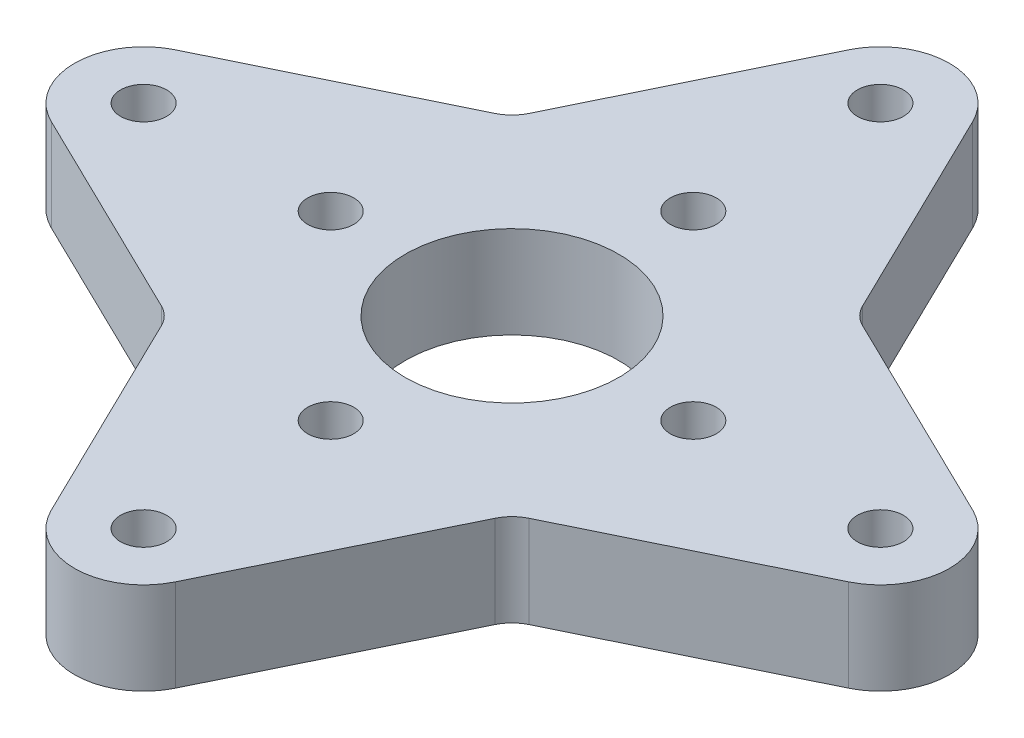
SolidWorks part; units mm, degrees
ref_plane "Front Plane" through (0, 0, 0) normal (0, 0, 1) x (1, 0, 0)
ref_plane "Top Plane" through (0, 0, 0) normal (0, 1, 0) x (1, 0, 0)
ref_plane "Right Plane" through (0, 0, 0) normal (1, 0, 0) x (0, 0, -1)
sketch "Sketch1" plane through (0, 0, 0) normal (0, 1, 0) x (1, 0, 0)
  line L0 (4.2813, 27.4861) -> (11.5, 12.6708)
  line L1 (0, 25.4) -> (0, 0) construction
  line L2 (-4.2813, 27.4861) -> (-11.5, 12.6708)
  line L3 (27.4861, 4.2813) -> (12.6708, 11.5)
  line L4 (27.4861, -4.2813) -> (12.6708, -11.5)
  line L5 (4.2813, -27.4861) -> (11.5, -12.6708)
  line L6 (-4.2813, -27.4861) -> (-11.5, -12.6708)
  line L7 (-27.4861, -4.2813) -> (-12.6708, -11.5)
  line L8 (-27.4861, 4.2813) -> (-12.6708, 11.5)
  line L9 (0, 0) -> (-34.9132, 34.9132) construction
  circle A0 centre (0, 0) radius 7.366
  circle A1 centre (0, 25.4) radius 1.5875
  circle A2 centre (0, 12.5) radius 1.5875
  arc A3 (4.2813, 27.4861) -> (-4.2813, 27.4861) centre (0, 25.4) ccw
  arc A4 (12.6708, -11.5) -> (11.5, -12.6708) centre (13.7834, -13.7834) ccw
  circle A5 centre (12.5, 0) radius 1.5875
  circle A6 centre (25.4, 0) radius 1.5875
  arc A7 (27.4861, -4.2813) -> (27.4861, 4.2813) centre (25.4, 0) ccw
  arc A8 (4.2813, -27.4861) -> (-4.2813, -27.4861) centre (0, -25.4) cw
  arc A9 (-12.6708, -11.5) -> (-11.5, -12.6708) centre (-13.7834, -13.7834) cw
  circle A10 centre (0, -25.4) radius 1.5875
  circle A11 centre (0, -12.5) radius 1.5875
  circle A12 centre (-12.5, 0) radius 1.5875
  circle A13 centre (-25.4, 0) radius 1.5875
  arc A14 (11.5, 12.6708) -> (12.6708, 11.5) centre (13.7834, 13.7834) ccw
  arc A15 (-12.6708, 11.5) -> (-11.5, 12.6708) centre (-13.7834, 13.7834) ccw
  arc A16 (-27.4861, -4.2813) -> (-27.4861, 4.2813) centre (-25.4, 0) cw
  dimension "D2" = 3.175
  dimension "D3" = 3.175
  dimension "D4" = 9.525
  dimension "D6" = 2.54
  dimension "D1" = 12.5
  dimension "D5" = 25.4
  dimension "D7" = 45
extrude "Boss-Extrude1" add sketch "Sketch1" along normal blind 6.35
chamfer "Chamfer1" distance 2.75 angle 45 4 edges at (0, 0, 10.9125) (-12.5, 0, -1.5875) (0, 0, -10.9125) (12.5, 0, 1.5875)
ref_plane "Plane1" through (0, 3.175, 0) normal (0, 1, 0) x (-1, 0, 0)
